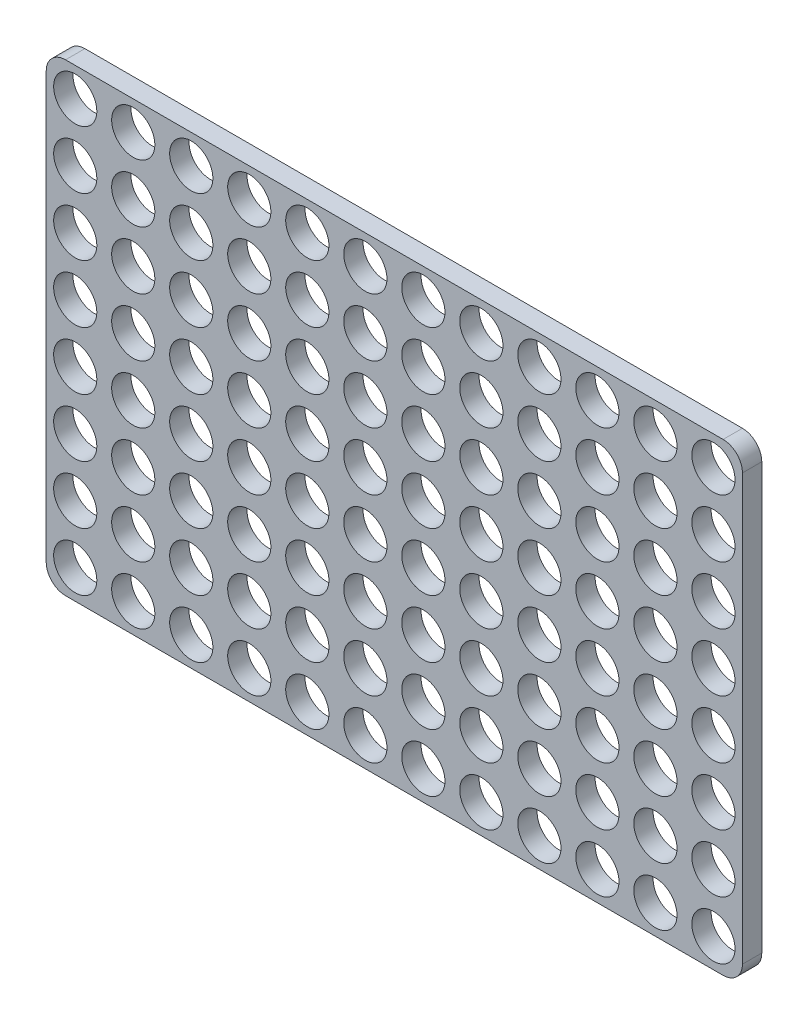
SolidWorks part; units mm, degrees
material "ABS"
ref_plane "Ebene vorne" through (0, 0, 0) normal (0, 0, 1) x (1, 0, 0)
ref_plane "Ebene oben" through (0, 0, 0) normal (0, 1, 0) x (1, 0, 0)
ref_plane "Ebene rechts" through (0, 0, 0) normal (1, 0, 0) x (0, 0, -1)
sketch "Skizze1" plane through (0, 0, 0) normal (0, 0, 1) x (1, 0, 0)
  line L0 (4.5, 4.5) -> (4.5, 9) construction
  line L1 (0, 0) -> (9, 0)
  line L2 (0, 0) -> (0, 9)
  line L3 (0, 9) -> (9, 9)
  line L4 (9, 0) -> (9, 9)
  line L5 (4.5, 4.5) -> (9, 4.5) construction
  circle A0 centre (4.5, 4.5) radius 3.35
  dimension "D1" = 9
  dimension "D3" = 6.7
  dimension "D2" = 9
extrude "Aufsatz-Linear austragen1" add sketch "Skizze1" along normal blind 3
pattern_linear "Lineares Muster1" count 12 spacing 9 along (1, 0, 0) count 8 spacing 9 along (0, 1, 0) of "Aufsatz-Linear austragen1"
fillet "Verrundung1" radius 3 4 edges at (108, 72, 1.5) (108, 0, 1.5) (0, 0, 1.5) (0, 72, 1.5)
